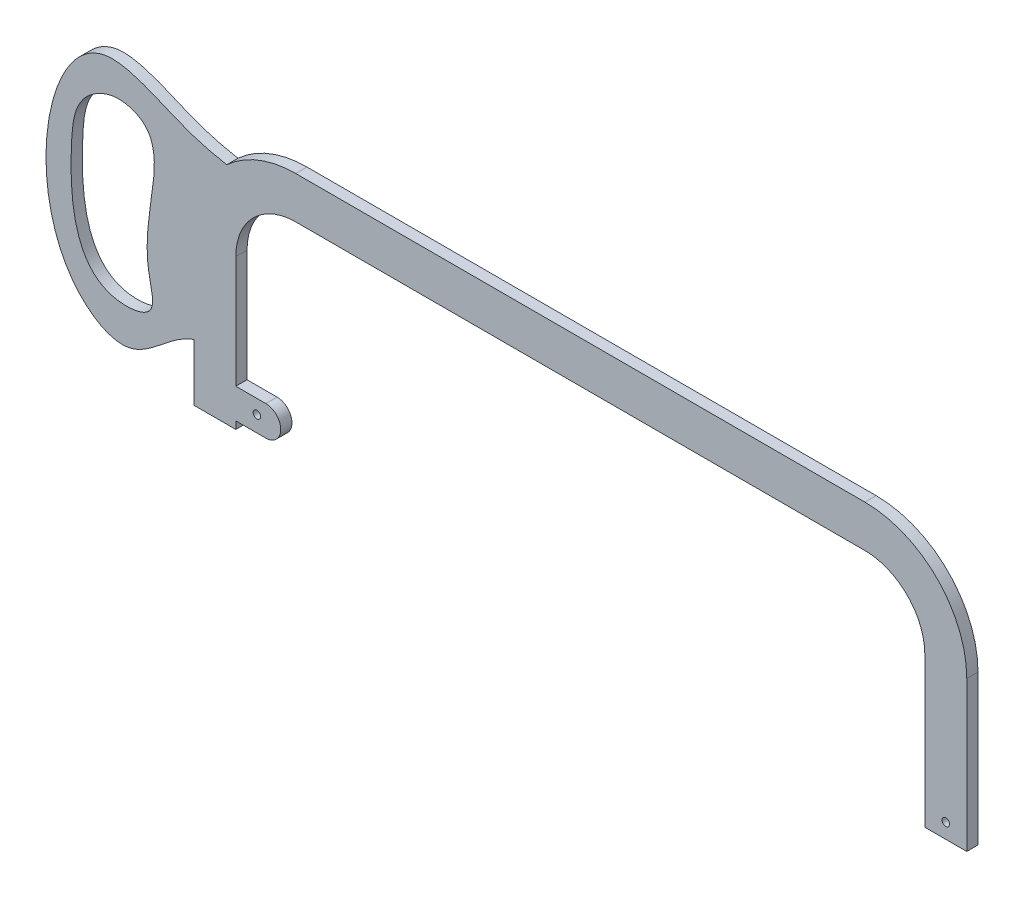
SolidWorks part; units mm, degrees
ref_plane "Front Plane" through (0, 0, 0) normal (0, 0, 1) x (1, 0, 0)
ref_plane "Top Plane" through (0, 0, 0) normal (0, 1, 0) x (1, 0, 0)
ref_plane "Right Plane" through (0, 0, 0) normal (1, 0, 0) x (0, 0, -1)
sketch "Sketch2" plane through (0, 0, 0) normal (0, 0, 1) x (1, 0, 0)
  line L0 (-176.2528, 0) -> (-176.2528, 63.5)
  line L1 (-150.8528, 88.9) -> (90.4472, 88.9)
  line L2 (115.8472, 63.5) -> (115.8472, 0)
  line L3 (115.8472, 0) -> (133.6272, 0)
  line L4 (133.6272, 0) -> (133.6272, 63.5)
  line L5 (90.4472, 106.68) -> (-150.8528, 106.68)
  line L6 (-194.0328, 63.5) -> (-194.0328, 0)
  line L7 (-194.0328, 0) -> (-176.2528, 0)
  arc A0 (-176.2528, 63.5) -> (-150.8528, 88.9) centre (-150.8528, 63.5) cw
  arc A1 (115.8472, 63.5) -> (90.4472, 88.9) centre (90.4472, 63.5) ccw
  arc A2 (-194.0328, 63.5) -> (-150.8528, 106.68) centre (-150.8528, 63.5) cw
  arc A3 (133.6272, 63.5) -> (90.4472, 106.68) centre (90.4472, 63.5) ccw
  dimension "D4" = 63.5
  dimension "D1" = 17.78
  dimension "D2" = 17.78
  dimension "D3" = 241.3
extrude "Extrude1" add sketch "Sketch2" along normal mid plane 4.7625
sketch "Sketch4" plane through (0, 0, 2.3813) normal (0, 0, 1) x (1, 0, 0)
  line L0 (-176.2528, 3.175) -> (-163.5528, 3.175)
  line L1 (-176.2528, 0) -> (-176.2528, 63.5) construction
  line L2 (-176.2528, 15.875) -> (-163.5528, 15.875)
  line L3 (-194.0328, 0) -> (-176.2528, 0) construction
  line L4 (-176.2528, 15.875) -> (-176.2528, 3.175)
  arc A0 (-163.5528, 3.175) -> (-163.5528, 15.875) centre (-163.5528, 9.525) ccw
  dimension "D1" = 12.7
  dimension "D2" = 3.175
  dimension "D3" = 12.7
extrude "Extrude2" add sketch "Sketch4" against normal up to surface (4.7625 mm away) up to face at (-30.2028, 56.1306, -2.3813)
sketch "Sketch5" plane through (0, 0, 2.3813) normal (0, 0, 1) x (1, 0, 0)
  line L0 (133.6272, 0) -> (133.6272, 63.5) construction
  circle A0 centre (-167.3363, 9.9386) radius 1.5875
  circle A1 centre (124.7372, 6.35) radius 1.5875
  arc A2 (115.8472, 63.5) -> (90.4472, 88.9) centre (90.4472, 63.5) ccw construction
  point P4 (90.4472, 63.5)
  dimension "D1" = 3.175
  dimension "D2" = 57.15
  dimension "D3" = 8.89
extrude "Cut-Extrude1" cut sketch "Sketch5" against normal through all
sketch "Sketch6" plane through (0, 0, 2.3813) normal (0, 0, 1) x (1, 0, 0)
  line L1 (-163.5001, 92.9767) -> (-185.371, 71.1058)
  line L2 (-185.371, 71.1058) -> (-185.371, 24.5413)
  spline S0 degree 3 poles (-163.5001, 92.9767) (-174.2158, 94.2301) (-196.7764, 96.8689) (-252.8592, 130.1247) (-269.4265, 29.7933) (-217.0907, -1.2909) (-200.7578, 26.3378) (-186.8997, 24.7198) (-185.371, 24.5413) knots 0 0 0 0 0.145422 0.306167 0.711218 0.81884 0.980016 1 1 1 1
  spline S1 degree 3 poles (-229.0238, 98.1269) (-244.4394, 89.2831) (-247.2836, 60.1055) (-244.9157, 18.8537) (-208.0817, 23.1237) (-220.298, 55.3932) (-201.0956, 90.7405) (-229.0238, 98.1269) (-244.4394, 89.2831) (-247.2836, 60.1055) knots -0.440904 -0.140512 -0.093904 0 0.110818 0.392382 0.473965 0.559096 0.859488 0.906096 1 1.110818 1.392382 1.473965 only from (-241.012, 88.8095) to (-241.012, 88.8095)
  point P2 (-249.3752, 94.5849)
extrude "Extrude3" add sketch "Sketch6" against normal up to surface (4.7625 mm away)
